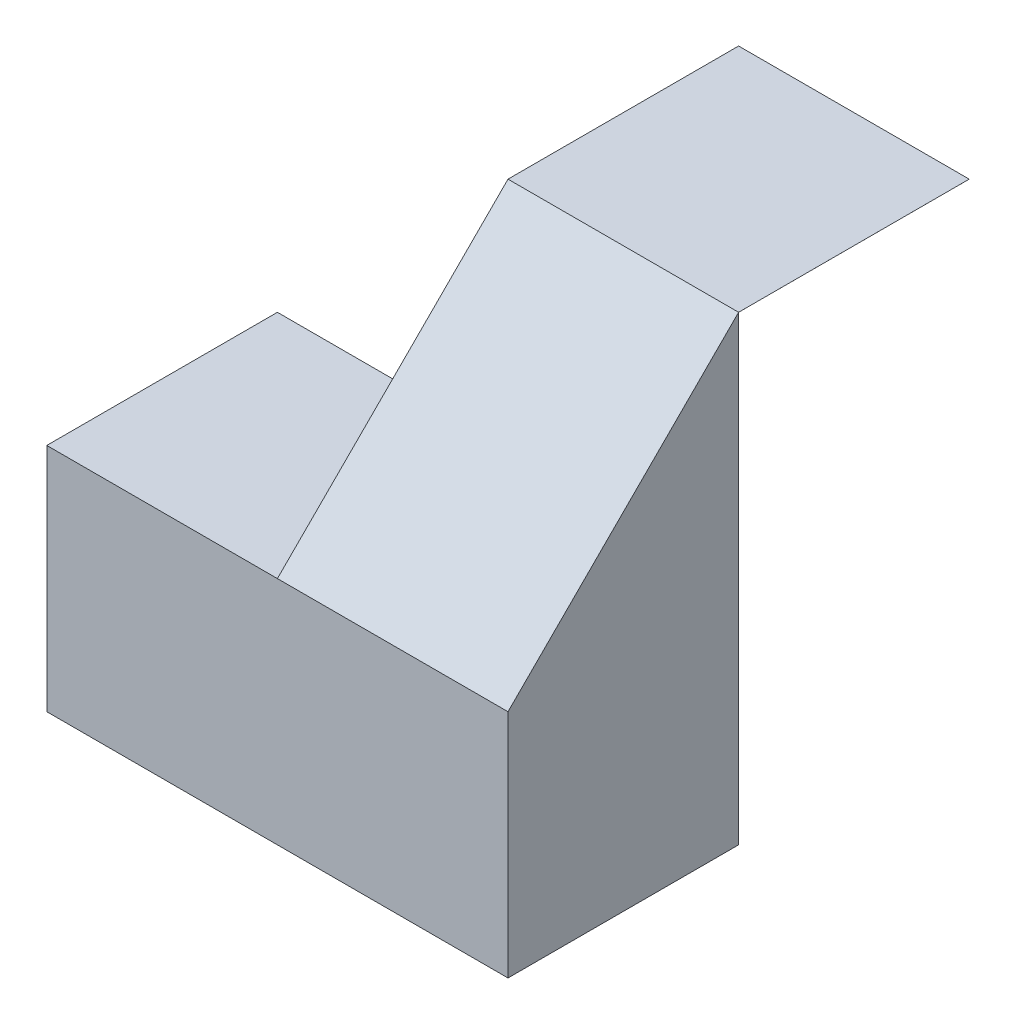
SolidWorks part; units mm, degrees
ref_plane "Front Plane" through (0, 0, 0) normal (0, 0, 1) x (1, 0, 0)
ref_plane "Top Plane" through (0, 0, 0) normal (0, 1, 0) x (1, 0, 0)
ref_plane "Right Plane" through (0, 0, 0) normal (1, 0, 0) x (0, 0, -1)
sketch "Sketch1" plane through (0, 0, 0) normal (0, 0, 1) x (1, 0, 0)
  line L1 (0, 0) -> (40, 0)
  line L2 (0, 0) -> (0, 40)
  line L3 (0, 40) -> (40, 40)
  line L4 (40, 0) -> (40, 40)
  dimension "D1" = 40
  dimension "D2" = 40
extrude "Boss-Extrude1" add sketch "Sketch1" along normal blind 40
sketch "Sketch2" plane through (0, 0, 40) normal (0, 0, 1) x (1, 0, 0)
  line L1 (0, 40) -> (20, 40)
  line L2 (0, 40) -> (0, 20)
  line L3 (0, 20) -> (20, 20)
  line L4 (20, 40) -> (20, 20)
  dimension "D1" = 20
  dimension "D2" = 20
extrude "Cut-Extrude1" cut sketch "Sketch2" against normal blind 40
sketch "Sketch3" plane through (20, 0, 0) normal (-1, 0, 0) x (0, 0, 1)
  line L0 (40, 20) -> (20, 40)
  line L1 (0, 40) -> (40, 40) construction
  line L2 (20, 40) -> (40, 40)
  line L3 (40, 40) -> (40, 20)
extrude "Cut-Extrude2" cut sketch "Sketch3" against normal blind 40
sketch "Sketch4" plane through (40, 0, 0) normal (1, 0, 0) x (0, 0, -1)
  line L1 (0, 0) -> (-20, 0)
  line L2 (0, 0) -> (0, 20)
  line L3 (0, 20) -> (-20, 20)
  line L4 (-20, 0) -> (-20, 20)
  dimension "D1" = 20
  dimension "D2" = 20
extrude "Cut-Extrude4" cut sketch "Sketch4" against normal blind 19.999
sketch "Sketch5" plane through (0, 0, 0) normal (0, 0, -1) x (-1, 0, 0)
  line L0 (-39.9999, 39.999) -> (-20.0001, 20.001)
  line L2 (-20.0001, 20.001) -> (-39.9999, 20.001)
  line L3 (-39.9999, 20.001) -> (-39.9999, 39.999)
  dimension "D1" = 19.998
  dimension "D2" = 0.001
  dimension "D3" = 0.0001
  dimension "D4" = 0.0001
extrude "Cut-Extrude6" cut sketch "Sketch5" against normal blind 19.999
sketch "Sketch6" plane through (39.9999, 0, 0) normal (-1, 0, 0) x (0, 0, 1)
  line L0 (0, 20.001) -> (19.999, 20.001)
  line L1 (0, 20.001) -> (0, 39.999)
  line L2 (0, 39.999) -> (20, 39.999)
  line L3 (20, 39.999) -> (19.999, 20.001)
  dimension "D1" = 20
extrude "Cut-Extrude7" cut sketch "Sketch6" against normal blind 19.999
sketch "Sketch7" plane through (0, 20.001, 0) normal (0, 1, 0) x (1, 0, 0)
  line L0 (40, 0) -> (40, -19.999) construction
  line L1 (20.0001, -19.999) -> (40, -19.999)
  line L2 (20.0001, -19.999) -> (20.0001, 0)
  line L3 (20.0001, 0) -> (40, 0)
  line L4 (40, -19.999) -> (40, 0)
  line L5 (40, 0) -> (20.0001, 0) construction
extrude "Cut-Extrude8" cut sketch "Sketch7" against normal blind 19.999
sketch "Sketch8" plane through (0, 0, 0) normal (-1, 0, 0) x (0, 0, 1)
  line L0 (0, 0) -> (20, 20)
  line L1 (0, 20) -> (40, 20) construction
  line L2 (20, 20) -> (0, 20)
  line L3 (0, 20) -> (0, 0)
extrude "Cut-Extrude9" cut sketch "Sketch8" against normal blind 19.999
sketch "Sketch9" plane through (20, 0, 0) normal (-1, 0, 0) x (0, 0, 1)
  line L0 (20, 40) -> (20, 20)
  line L1 (0, 20) -> (40, 20) construction
  line L2 (20, 20) -> (40, 20)
  line L3 (40, 20) -> (20, 40)
extrude "Cut-Extrude10" cut sketch "Sketch9" against normal blind 0.0001
